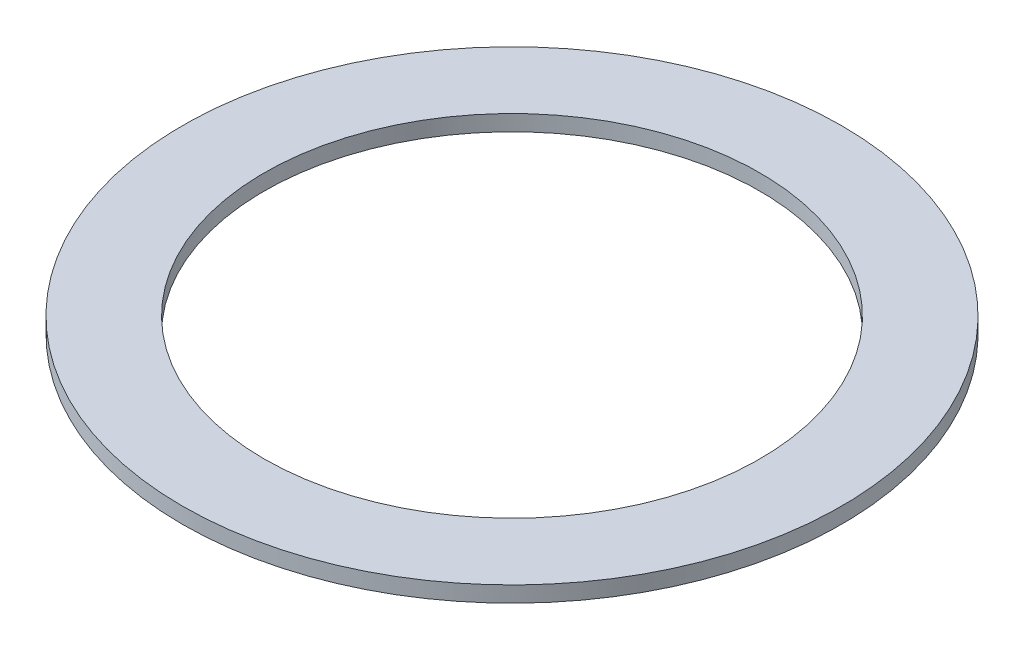
SolidWorks part; units mm, degrees
ref_plane "Front Plane" through (0, 0, 0) normal (0, 0, 1) x (1, 0, 0)
ref_plane "Top Plane" through (0, 0, 0) normal (0, 1, 0) x (1, 0, 0)
ref_plane "Right Plane" through (0, 0, 0) normal (1, 0, 0) x (0, 0, -1)
sketch "Sketch1" plane through (0, 0, 0) normal (0, 1, 0) x (1, 0, 0)
  circle A0 centre (0, 0) radius 2.3876
  circle A1 centre (0, 0) radius 3.175
  dimension "D1" = 4.7752
  dimension "D2" = 6.35
extrude "Boss-Extrude1" add sketch "Sketch1" along normal blind 0.1524
